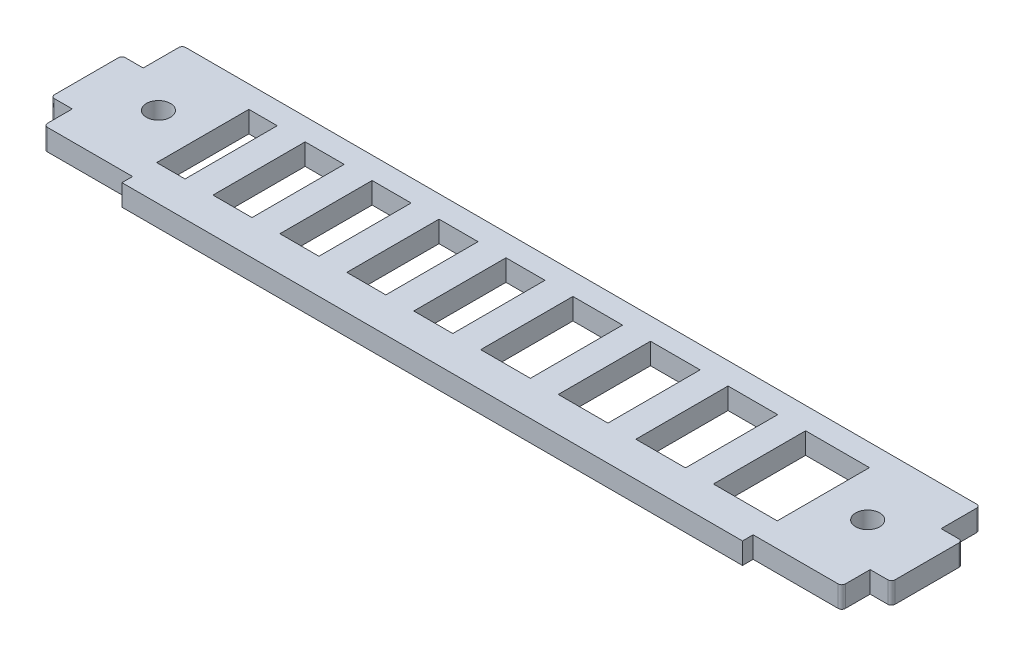
SolidWorks part; units mm, degrees
ref_plane "Спереди" through (0, 0, 0) normal (0, 0, 1) x (1, 0, 0)
ref_plane "Сверху" through (0, 0, 0) normal (0, 1, 0) x (1, 0, 0)
ref_plane "Справа" through (0, 0, 0) normal (1, 0, 0) x (0, 0, -1)
sketch "Эскиз1" plane through (0, 0, 0) normal (0, 1, 0) x (1, 0, 0)
  line L0 (0, -21) -> (0, 21.8864) construction
  line L1 (-43.75, -21) -> (43.75, -21)
  line L2 (43.75, -21) -> (43.75, -19.5)
  line L3 (43.75, -19.5) -> (56.25, -19.5)
  line L4 (56.25, -19.5) -> (56.25, -15.5)
  line L5 (56.25, -15.5) -> (59.25, -15.5)
  line L6 (59.25, -15.5) -> (59.25, -5.5)
  line L7 (59.25, -5.5) -> (56.25, -5.5)
  line L8 (56.25, -5.5) -> (56.25, 0)
  line L9 (56.25, 0) -> (-56.25, 0)
  line L10 (-56.25, -5.5) -> (-56.25, 0)
  line L11 (-59.25, -5.5) -> (-56.25, -5.5)
  line L12 (-59.25, -15.5) -> (-59.25, -5.5)
  line L13 (-56.25, -15.5) -> (-59.25, -15.5)
  line L14 (-56.25, -19.5) -> (-56.25, -15.5)
  line L15 (-43.75, -19.5) -> (-56.25, -19.5)
  line L16 (-43.75, -21) -> (-43.75, -19.5)
  line L17 (52.2732, -10.5) -> (61.8348, -10.5) construction
  line L18 (-26.375, -16.1) -> (-20.875, -16.1)
  line L19 (-35.8125, -3.1) -> (-30.3125, -3.1)
  line L20 (-35.8125, -3.1) -> (-35.8125, -16.1)
  line L21 (-35.8125, -16.1) -> (-30.3125, -16.1)
  line L22 (-30.3125, -3.1) -> (-30.3125, -16.1)
  line L23 (-35.8125, -3.1) -> (-30.3125, -16.1) construction
  line L24 (-35.8125, -16.1) -> (-30.3125, -3.1) construction
  line L25 (-26.375, -3.1) -> (-20.875, -3.1)
  line L26 (-20.875, -3.1) -> (-20.875, -16.1)
  line L27 (-26.375, -3.1) -> (-26.375, -16.1)
  line L28 (-16.9375, -16.1) -> (-11.4375, -16.1)
  line L29 (-16.9375, -3.1) -> (-11.4375, -3.1)
  line L30 (-11.4375, -3.1) -> (-11.4375, -16.1)
  line L31 (-16.9375, -3.1) -> (-16.9375, -16.1)
  line L32 (-7.5, -16.1) -> (-2, -16.1)
  line L33 (-7.5, -3.1) -> (-2, -3.1)
  line L34 (-2, -3.1) -> (-2, -16.1)
  line L35 (-7.5, -3.1) -> (-7.5, -16.1)
  line L60 (49.125, -3.1) -> (54.625, -3.1) [skipped]
  line L61 (49.125, -16.1) -> (54.625, -16.1) [skipped]
  line L62 (49.125, -3.1) -> (49.125, -16.1) [skipped]
  line L63 (54.625, -3.1) -> (54.625, -16.1) [skipped]
  line L64 (39.6875, -16.1) -> (45.1875, -16.1) [skipped]
  line L65 (39.6875, -3.1) -> (45.1875, -3.1) [skipped]
  line L66 (45.1875, -3.1) -> (45.1875, -16.1) [skipped]
  line L67 (39.6875, -3.1) -> (39.6875, -16.1) [skipped]
  line L68 (11.375, -16.1) -> (16.875, -16.1) [skipped]
  line L69 (11.375, -3.1) -> (16.875, -3.1) [skipped]
  line L70 (16.875, -3.1) -> (16.875, -16.1) [skipped]
  line L71 (20.8125, -16.1) -> (26.3125, -16.1) [skipped]
  line L72 (20.8125, -3.1) -> (26.3125, -3.1) [skipped]
  line L73 (26.3125, -3.1) -> (26.3125, -16.1) [skipped]
  line L74 (20.8125, -3.1) -> (20.8125, -16.1) [skipped]
  line L75 (30.25, -16.1) -> (35.75, -16.1) [skipped]
  line L76 (30.25, -3.1) -> (35.75, -3.1) [skipped]
  line L77 (35.75, -3.1) -> (35.75, -16.1) [skipped]
  line L78 (30.25, -3.1) -> (30.25, -16.1) [skipped]
  line L79 (11.375, -3.1) -> (11.375, -16.1) [skipped]
  line L80 (12.875, -3.1) -> (19.875, -3.1)
  line L81 (1.9375, -3.1) -> (8.9375, -3.1)
  line L82 (1.9375, -3.1) -> (1.9375, -16.1)
  line L83 (1.9375, -16.1) -> (8.9375, -16.1)
  line L84 (8.9375, -3.1) -> (8.9375, -16.1)
  line L85 (1.9375, -3.1) -> (8.9375, -16.1) construction
  line L86 (1.9375, -16.1) -> (8.9375, -3.1) construction
  line L87 (1.9375, -3.1) -> (1.9375, -16.1) [skipped]
  line L88 (1.9375, -3.1) -> (7.4375, -3.1) [skipped]
  line L89 (7.4375, -3.1) -> (7.4375, -16.1) [skipped]
  line L90 (1.9375, -16.1) -> (7.4375, -16.1) [skipped]
  line L91 (12.875, -3.1) -> (12.875, -16.1)
  line L92 (19.875, -3.1) -> (19.875, -16.1)
  line L93 (12.875, -16.1) -> (19.875, -16.1)
  line L94 (23.8125, -3.1) -> (30.8125, -3.1)
  line L95 (23.8125, -3.1) -> (23.8125, -16.1)
  line L96 (30.8125, -3.1) -> (30.8125, -16.1)
  line L97 (23.8125, -16.1) -> (30.8125, -16.1)
  line L103 (-11.4375, -16.1) -> (-7.5, -16.1) construction
  line L104 (-39.75, -16.1) -> (-35.8125, -16.1) construction
  line L108 (-43.75, -3.1) -> (-39.75, -3.1)
  line L113 (-43.75, -3.1) -> (-43.75, -16.1)
  line L114 (-43.75, -16.1) -> (-39.75, -16.1)
  line L119 (-39.75, -3.1) -> (-39.75, -16.1)
  line L120 (-43.75, -3.1) -> (-39.75, -16.1) construction
  line L121 (1.9375, -16.1) -> (-2, -16.1) construction
  line L122 (12.875, -16.1) -> (8.9375, -16.1) construction
  line L123 (-43.75, -16.1) -> (-39.75, -3.1) construction
  line L124 (34.75, -3.1) -> (41.75, -3.1) [skipped]
  line L125 (34.75, -3.1) -> (34.75, -16.1) [skipped]
  line L126 (34.75, -16.1) -> (41.75, -16.1) [skipped]
  line L127 (41.75, -3.1) -> (41.75, -16.1) [skipped]
  line L128 (30.8125, -16.1) -> (34.75, -16.1) construction
  line L129 (34.75, -3.1) -> (43.75, -3.1)
  line L130 (34.75, -3.1) -> (34.75, -16.1)
  line L131 (34.75, -16.1) -> (43.75, -16.1)
  line L132 (43.75, -3.1) -> (43.75, -16.1)
  line L133 (34.75, -3.1) -> (43.75, -16.1) construction
  line L134 (34.75, -16.1) -> (43.75, -3.1) construction
  point P14 (50, -9.6)
  point P15 (-33.0625, -9.6)
  point P18 (0, 0)
  point P25 (-50, -9.6)
  point P35 (5.4375, -9.6)
  point P47 (39.25, -9.6)
  point P67 (-41.75, -9.6)
  dimension "D10" = 4
  dimension "D1" = 3
  dimension "D2" = 10
  dimension "D3" = 12.5
  dimension "D4" = 21
  dimension "D5" = 19.5
  dimension "D6" = 10.5
  dimension "D7" = 100
  dimension "D8" = 6.25
  dimension "D9" = 9.6
  dimension "D12" = 5.5
  dimension "D13" = 10
  dimension "D11" = 13
  dimension "D14" = 7
  dimension "D15" = 6.25
  dimension "D16" = 9
  dimension "D18" = 6.25
  dimension "D17" = 4
extrude "Бобышка-Вытянуть1" add sketch "Эскиз1" along normal blind 3
hole_wizard "Отверстие с зазором M31" positions "Эскиз2" profile "Эскиз3" hole size "M3" standard "IS"
sketch "Эскиз2" plane through (0, 3, 0) normal (0, 1, 0) x (1, 0, 0)
  point P0 (50, -9.6)
  point P2 (-50, -9.6)
sketch "Эскиз3" plane through (50, 3, 9.6) normal (1, 0, 0) x (0, 0, 1)
  line L0 (0, 0) -> (0, 11.0215)
  line L1 (0, 11.0215) -> (1.7, 10)
  line L2 (1.7, 10) -> (1.7, 0)
  line L5 (1.7, 0) -> (0, 0)
  line L10 (0, 11.0215) -> (-1.7, 10) construction
  line L11 (0, -6.35) -> (0, 107.95) construction
  dimension "Диаметр отверстия" = 3.4
  dimension "Глубина отверстия" = 10
  dimension "Угол заточки сверла" = 118
fillet "Скругление1" radius 0.5 8 edges at (-59.25, 1.5, 5.5) (-59.25, 1.5, 15.5) (59.25, 1.5, 5.5) (59.25, 1.5, 15.5) (-56.25, 1.5, 0) (-56.25, 1.5, 19.5) (56.25, 1.5, 0) (56.25, 1.5, 19.5)
